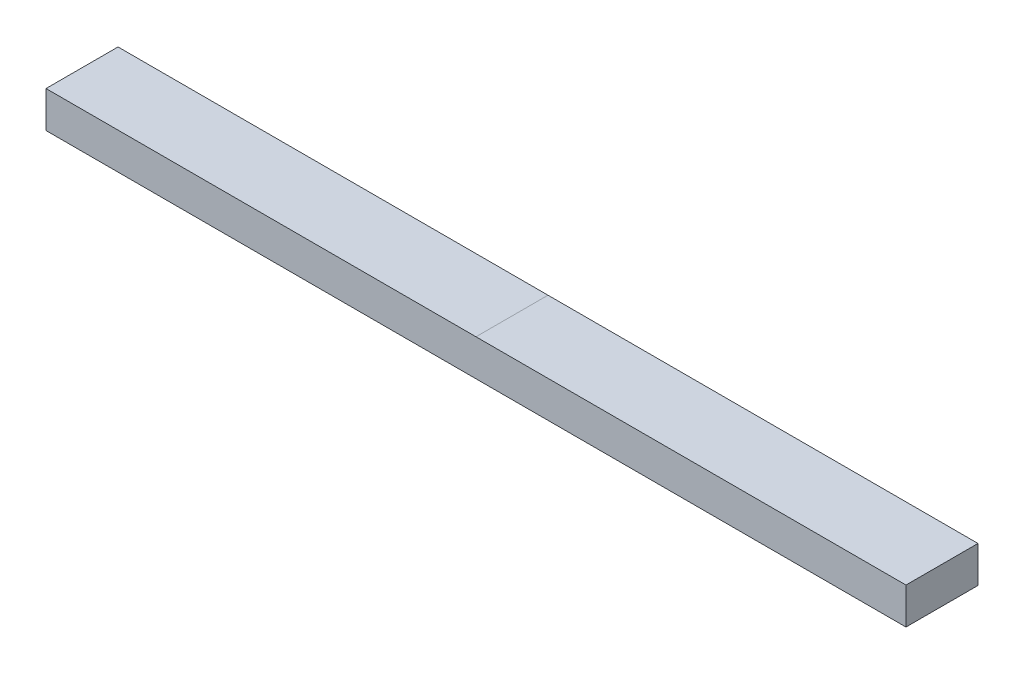
SolidWorks part; units mm, degrees
material "6061-T6 (SS)"
ref_plane "Front Plane" through (0, 0, 0) normal (0, 0, 1) x (1, 0, 0)
ref_plane "Top Plane" through (0, 0, 0) normal (0, 1, 0) x (1, 0, 0)
ref_plane "Right Plane" through (0, 0, 0) normal (1, 0, 0) x (0, 0, -1)
sketch "Sketch1" plane through (0, 0, 0) normal (1, 0, 0) x (0, 0, -1)
  line L1 (-6.3817, -3.2258) -> (6.3818, -3.2258)
  line L2 (-6.3817, -3.2258) -> (-6.3817, 3.2258)
  line L3 (-6.3817, 3.2258) -> (6.3817, 3.2258)
  line L4 (6.3818, -3.2258) -> (6.3817, 3.2258)
  line L5 (-6.3817, -3.2258) -> (6.3817, 3.2258) construction
  line L6 (-6.3817, 3.2258) -> (6.3818, -3.2258) construction
  point P0 (0, 0)
  dimension "D1" = 6.4516
  dimension "D2" = 12.7635
extrude "Boss-Extrude1" add sketch "Sketch1" along normal mid plane 152.4 contours L3 L4 L1 L2
ref_plane "Plane1" through (63.5, 0, 0) normal (1, 0, 0) x (0, 0, -1)
ref_plane "Plane2" through (-63.5, 0, 0) normal (1, 0, 0) x (0, 0, -1)
split line "Split Line1"
split line "Split Line3"
